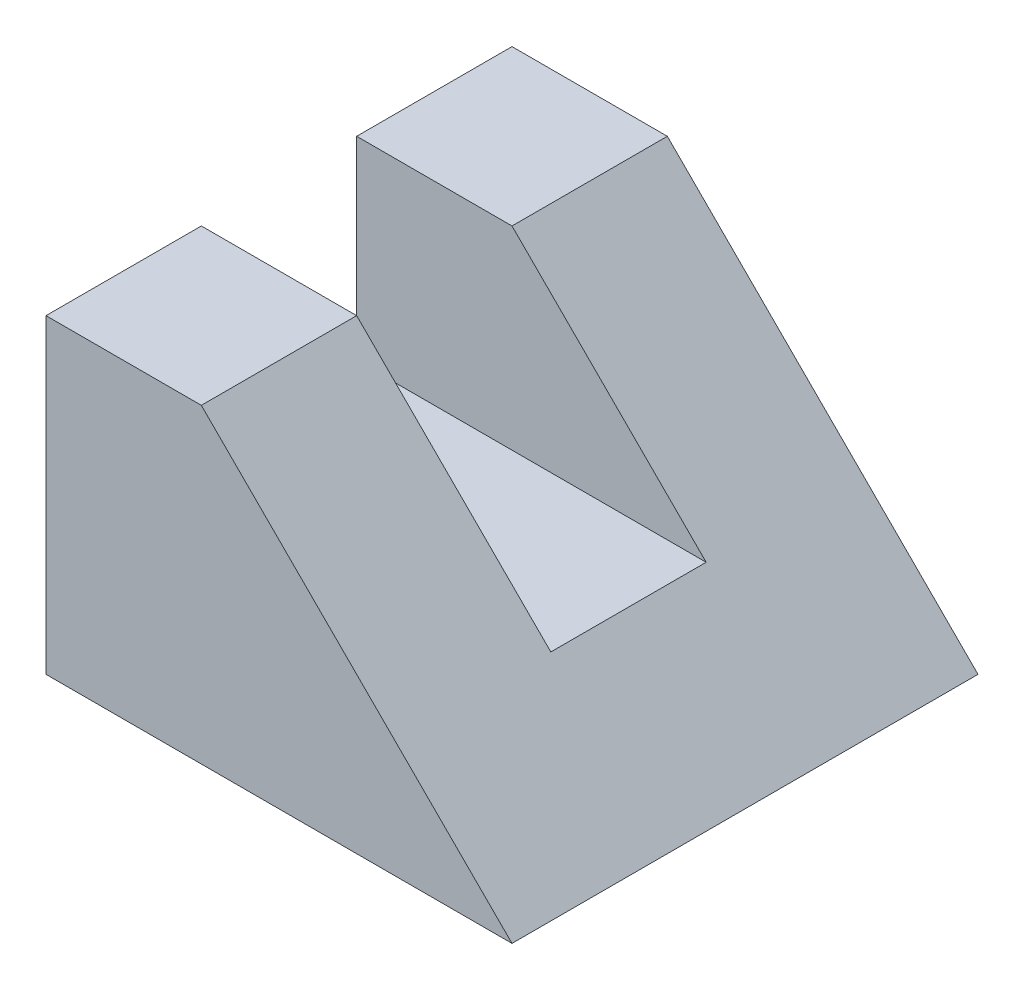
SolidWorks part; units mm, degrees
ref_plane "Front Plane" through (0, 0, 0) normal (0, 0, 1) x (1, 0, 0)
ref_plane "Top Plane" through (0, 0, 0) normal (0, 1, 0) x (1, 0, 0)
ref_plane "Right Plane" through (0, 0, 0) normal (1, 0, 0) x (0, 0, -1)
sketch "Sketch1" plane through (0, 0, 0) normal (0, 0, 1) x (1, 0, 0)
  line L0 (-300, 400) -> (-300, 0)
  line L1 (-300, 0) -> (300, 0)
  line L2 (300, 0) -> (-100, 400)
  line L3 (-100, 400) -> (-300, 400)
  dimension "D1" = 400
  dimension "D2" = 600
  dimension "D3" = 200
  dimension "D4" = 400
  dimension "D5" = 300
extrude "Boss-Extrude1" add sketch "Sketch1" along normal blind 300
sketch "Sketch2" plane through (0, 400, 0) normal (0, 1, 0) x (1, 0, 0)
  line L1 (-300, 0) -> (300, 0)
  line L2 (-300, 0) -> (-300, -100)
  line L3 (-300, -100) -> (300, -100)
  line L4 (300, 0) -> (300, -100)
  dimension "D1" = 100
  dimension "D2" = 600
extrude "Cut-Extrude1" cut sketch "Sketch2" against normal blind 250
mirror "Mirror1" about plane through (0, 0, 0) normal (0, 0, 1) of "Cut-Extrude1", "Boss-Extrude1"
